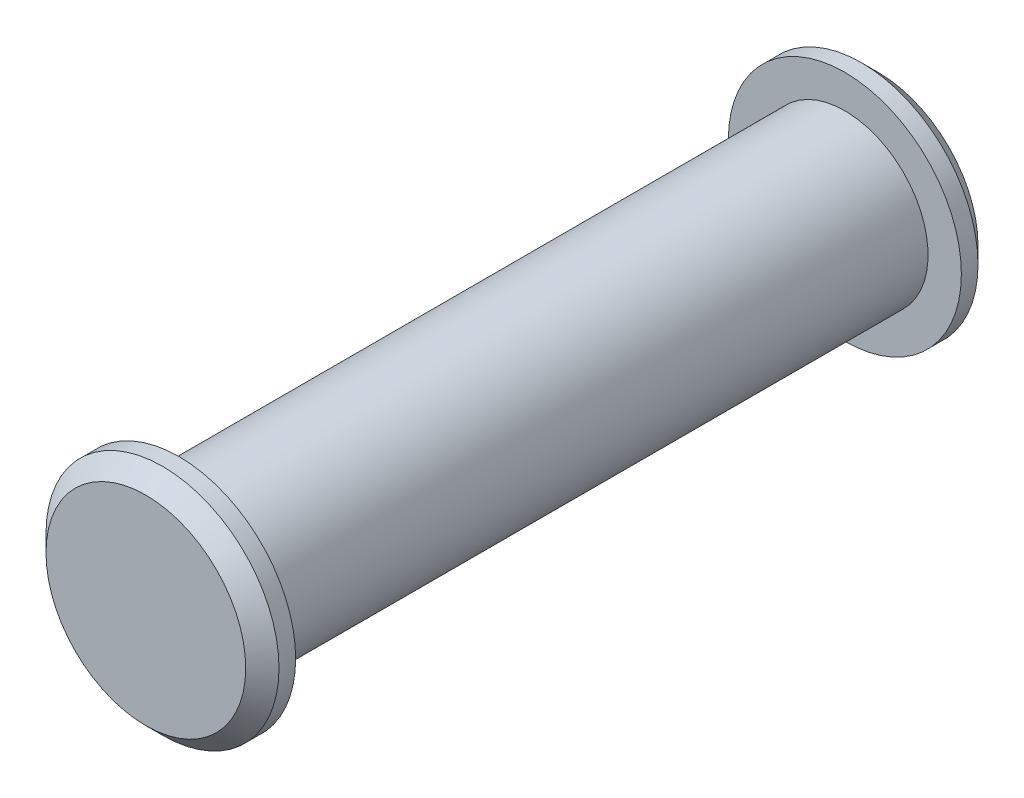
SolidWorks part; units mm, degrees
ref_plane "Front Plane" through (0, 0, 0) normal (0, 0, 1) x (1, 0, 0)
ref_plane "Top Plane" through (0, 0, 0) normal (0, 1, 0) x (1, 0, 0)
ref_plane "Right Plane" through (0, 0, 0) normal (1, 0, 0) x (0, 0, -1)
sketch "Sketch1" plane through (0, 0, 0) normal (0, 0, 1) x (1, 0, 0)
  circle A0 centre (0, 0) radius 2.5
  dimension "D1" = 5
extrude "Boss-Extrude1" add sketch "Sketch1" along normal mid plane 20
sketch "Sketch2" plane through (0, 0, 10) normal (0, 0, 1) x (1, 0, 0)
  circle A0 centre (0, 0) radius 3.5
  dimension "D1" = 7
extrude "Boss-Extrude2" add sketch "Sketch2" along normal blind 1
mirror "Mirror1" about plane through (0, 0, 0) normal (0, 0, 1) of "Boss-Extrude2"
chamfer "Chamfer1" distance 0.5 angle 45 2 edges at (3.5, 0, -11) (3.5, 0, 11)
